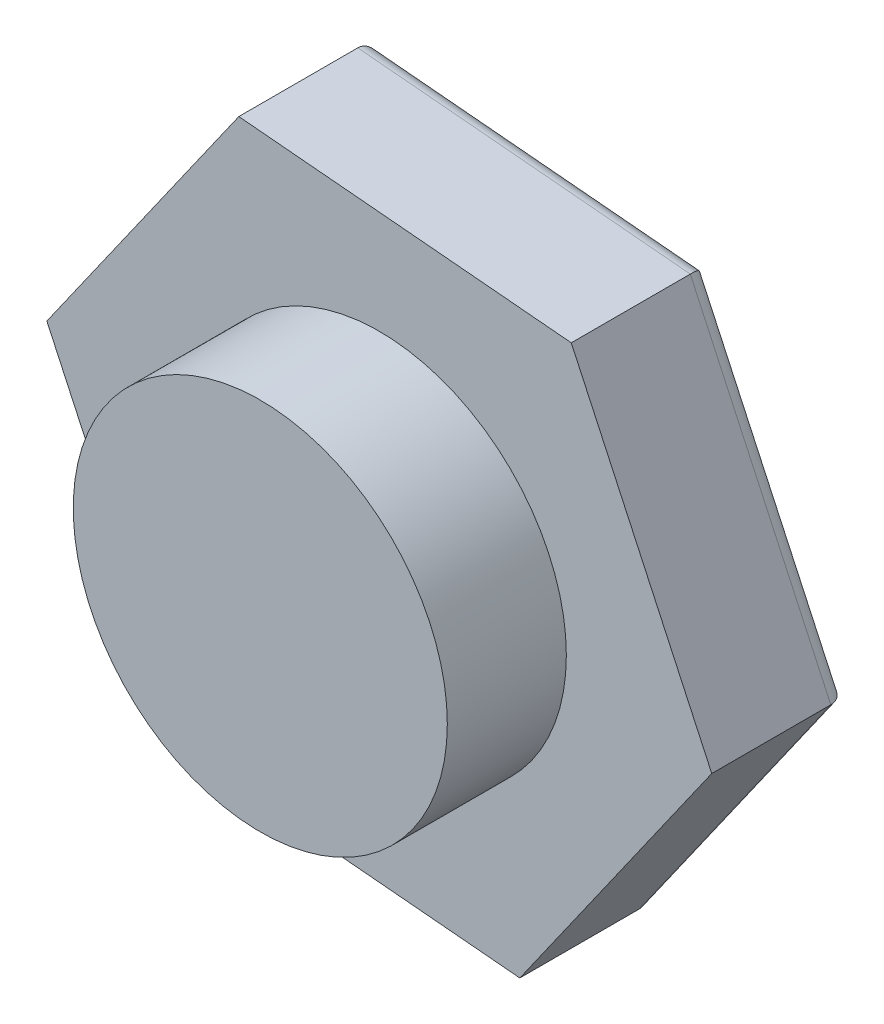
SolidWorks part; units mm, degrees
material "2014-T6"
ref_plane "Piano frontale" through (0, 0, 0) normal (0, 0, 1) x (1, 0, 0)
ref_plane "Piano superiore" through (0, 0, 0) normal (0, 1, 0) x (1, 0, 0)
ref_plane "Piano destro" through (0, 0, 0) normal (1, 0, 0) x (0, 0, -1)
sketch "Schizzo1" plane through (0, 0, 0) normal (0, 0, 1) x (1, 0, 0)
  circle A0 centre (0, 0) radius 11
  dimension "D1" = 22
extrude "Estrusione-Estrusione1" add sketch "Schizzo1" along normal blind 7
cosmetic thread "Filettatura cosmetica1"
sketch "Schizzo2" plane through (0, 0, 0) normal (0, 0, -1) x (-1, 0, 0)
  line L1 (-19.552, -1.7473) -> (-8.2628, -17.8062)
  line L2 (-8.2628, -17.8062) -> (11.2892, -16.0589)
  line L3 (11.2892, -16.0589) -> (19.552, 1.7473)
  line L4 (19.552, 1.7473) -> (8.2628, 17.8062)
  line L5 (8.2628, 17.8062) -> (-11.2892, 16.0589)
  line L6 (-11.2892, 16.0589) -> (-19.552, -1.7473)
  circle A0 centre (0, 0) radius 17 construction
  dimension "D1" = 34
extrude "Estrusione-Estrusione2" add sketch "Schizzo2" along normal blind 8
fillet "Raccordo1" radius 1 6 edges at (1.5132, 16.9325, -8) (-13.9074, 9.7767, -8) (-15.4206, -7.1558, -8) (-1.5132, -16.9325, -8) (13.9074, -9.7767, -8) (15.4206, 7.1558, -8)
ref_plane "Piano1" through (0, 0, 10) normal (0, 0, 1) x (1, 0, 0)
